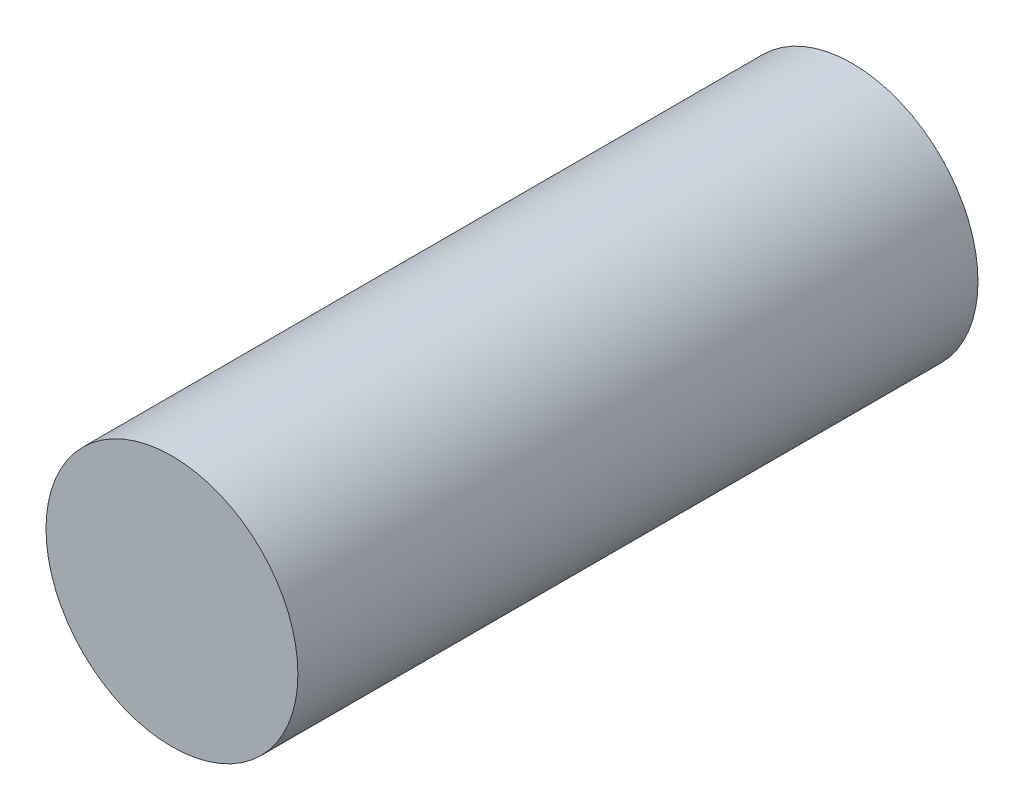
SolidWorks part; units mm, degrees
ref_plane "Front Plane" through (0, 0, 0) normal (0, 0, 1) x (1, 0, 0)
ref_plane "Top Plane" through (0, 0, 0) normal (0, 1, 0) x (1, 0, 0)
ref_plane "Right Plane" through (0, 0, 0) normal (1, 0, 0) x (0, 0, -1)
sketch "Sketch1" plane through (0, 0, 0) normal (0, 0, 1) x (1, 0, 0)
  circle A0 centre (0, 0) radius 6.35
  dimension "D1" = 12.7
extrude "Boss-Extrude1" add sketch "Sketch1" along normal blind 34.29
